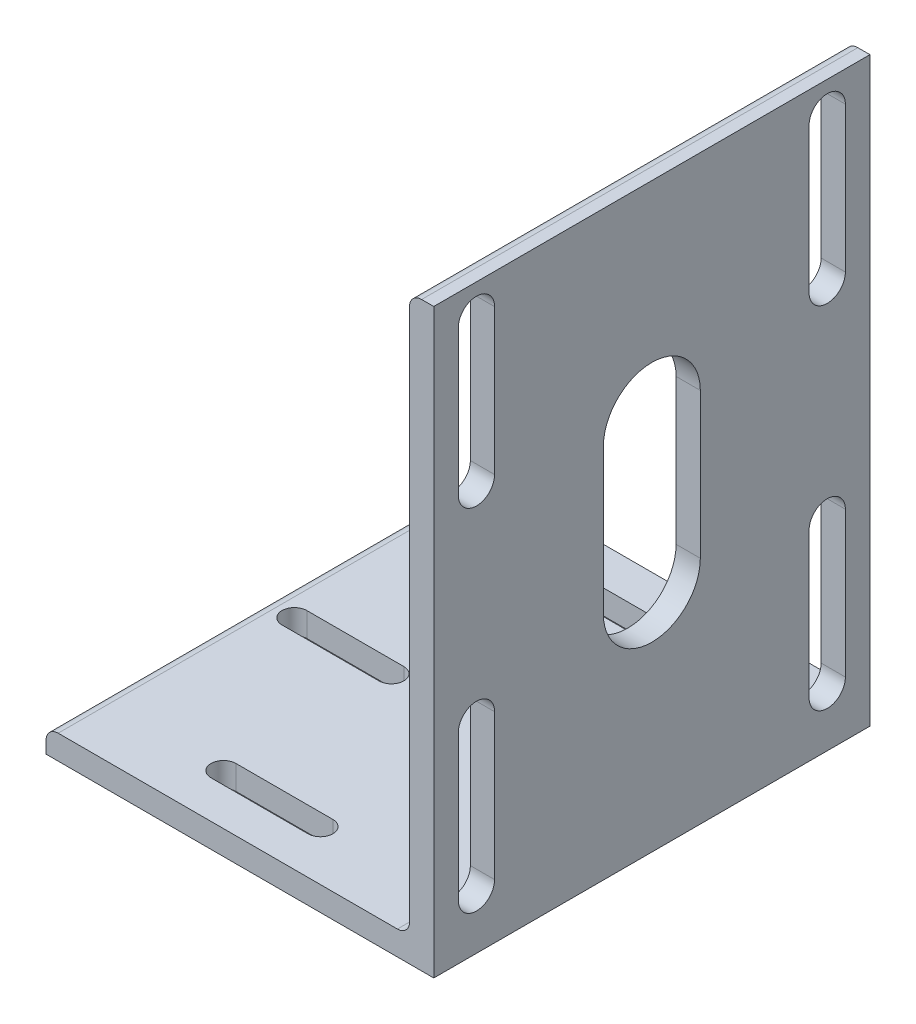
SolidWorks part; units mm, degrees
ref_plane "Front Plane" through (0, 0, 0) normal (0, 0, 1) x (1, 0, 0)
ref_plane "Top Plane" through (0, 0, 0) normal (0, 1, 0) x (1, 0, 0)
ref_plane "Right Plane" through (0, 0, 0) normal (1, 0, 0) x (0, 0, -1)
sketch "Sketch2" plane through (0, 0, 0) normal (0, 0, 1) x (1, 0, 0)
  line L0 (-50.8, 0) -> (50.8, 0)
  line L1 (50.8, 0) -> (50.8, 152.4)
  line L2 (50.8, 152.4) -> (44.45, 152.4) construction
  line L3 (44.45, 149.225) -> (44.45, 9.525)
  line L4 (41.275, 6.35) -> (-47.625, 6.35)
  line L5 (-50.8, 0) -> (-50.8, 6.35) construction
  line L6 (47.625, 152.4) -> (50.8, 152.4)
  line L7 (-50.8, 3.175) -> (-50.8, 0)
  arc A0 (44.45, 149.225) -> (47.625, 152.4) centre (47.625, 149.225) cw
  arc A1 (-50.8, 3.175) -> (-47.625, 6.35) centre (-47.625, 3.175) cw
  arc A2 (44.45, 9.525) -> (41.275, 6.35) centre (41.275, 9.525) cw
  dimension "Vert" = 152.4
  dimension "Horz" = 101.6
  dimension "Thickness" = 6.35
extrude "Boss-Extrude1" add sketch "Sketch2" along normal mid plane 304.8
ref_plane "Contact Plane 1" through (0, 6.35, 0) normal (0, 1, 0) x (1, 0, 0)
ref_plane "Contact Plane 2" through (44.45, 0, 0) normal (-1, 0, 0) x (0, 0, 1)
ref_plane "Plane1" through (0, 0, -38.1) normal (0, 0, -1) x (-1, 0, 0)
other "SurfaceCut1"
sketch "Sketch3" plane through (50.8, 0, 0) normal (1, 0, 0) x (0, 0, -1)
  line L0 (152.4, 79.375) -> (95.25, 79.375) construction
  line L1 (152.4, 0) -> (152.4, 152.4) construction
  line L2 (95.25, 79.375) -> (38.1, 79.375) construction
  line L3 (38.1, 152.4) -> (38.1, 0) construction
  line L4 (95.25, 152.4) -> (95.25, 6.35) construction
  line L5 (38.1, 152.4) -> (152.4, 152.4) construction
  line L6 (95.25, 79.375) -> (49.2881, 33.4131) construction
  line L7 (141.2119, 144.3869) -> (141.2119, 106.2869) construction
  line L8 (145.9619, 144.3869) -> (145.9619, 106.2869)
  line L9 (136.4619, 144.3869) -> (136.4619, 106.2869)
  line L10 (141.2119, 52.4631) -> (141.2119, 14.3631) construction
  line L11 (145.9619, 52.4631) -> (145.9619, 14.3631)
  line L12 (136.4619, 52.4631) -> (136.4619, 14.3631)
  line L13 (141.2119, 125.3369) -> (95.25, 79.375) construction
  line L14 (95.25, 79.375) -> (141.2119, 33.4131) construction
  line L15 (49.2881, 125.3369) -> (95.25, 79.375) construction
  line L16 (49.2881, 52.4631) -> (49.2881, 14.3631) construction
  line L17 (44.5381, 52.4631) -> (44.5381, 14.3631)
  line L18 (54.0381, 52.4631) -> (54.0381, 14.3631)
  line L19 (49.2881, 144.3869) -> (49.2881, 106.2869) construction
  line L20 (44.5381, 144.3869) -> (44.5381, 106.2869)
  line L21 (54.0381, 144.3869) -> (54.0381, 106.2869)
  line L22 (95.25, 98.425) -> (95.25, 60.325) construction
  line L23 (107.95, 98.425) -> (107.95, 60.325)
  line L24 (82.55, 98.425) -> (82.55, 60.325)
  circle A0 centre (95.25, 79.375) radius 65 construction
  arc A1 (145.9619, 144.3869) -> (136.4619, 144.3869) centre (141.2119, 144.3869) ccw
  arc A2 (136.4619, 106.2869) -> (145.9619, 106.2869) centre (141.2119, 106.2869) ccw
  arc A3 (145.9619, 52.4631) -> (136.4619, 52.4631) centre (141.2119, 52.4631) ccw
  arc A4 (136.4619, 14.3631) -> (145.9619, 14.3631) centre (141.2119, 14.3631) ccw
  arc A5 (44.5381, 52.4631) -> (54.0381, 52.4631) centre (49.2881, 52.4631) cw
  arc A6 (54.0381, 14.3631) -> (44.5381, 14.3631) centre (49.2881, 14.3631) cw
  arc A7 (44.5381, 144.3869) -> (54.0381, 144.3869) centre (49.2881, 144.3869) cw
  arc A8 (54.0381, 106.2869) -> (44.5381, 106.2869) centre (49.2881, 106.2869) cw
  arc A9 (107.95, 98.425) -> (82.55, 98.425) centre (95.25, 98.425) ccw
  arc A10 (82.55, 60.325) -> (107.95, 60.325) centre (95.25, 60.325) ccw
  point P14 (141.2119, 125.3369)
  point P17 (95.25, 79.375)
  point P22 (141.2119, 33.4131)
  point P34 (49.2881, 33.4131)
  point P41 (49.2881, 125.3369)
  point P48 (95.25, 79.375)
  dimension "D1" = 130
  dimension "D3" = 4.75
  dimension "D5" = 12.7
  dimension "D2" = 6.35
  dimension "D4" = 38.1
  dimension "D6" = 38.1
extrude "Cut-Extrude1" cut sketch "Sketch3" against normal through all
ref_plane "Plane2" through (0, 0, -95.25) normal (0, 0, -1) x (-1, 0, 0)
sketch "Sketch4" plane through (0, 6.35, 0) normal (0, 1, 0) x (1, 0, 0)
  line L0 (41.275, 95.25) -> (-50.8, 95.25) construction
  line L1 (41.275, 38.1) -> (41.275, 152.4) construction
  line L2 (-50.8, 38.1) -> (-50.8, 152.4) construction
  line L3 (-42.8625, 95.25) -> (-17.4625, 95.25) construction
  line L4 (-42.8625, 98.5139) -> (-17.4625, 98.5139)
  line L5 (-42.8625, 91.9861) -> (-17.4625, 91.9861)
  line L6 (7.9375, 95.25) -> (33.3375, 95.25) construction
  line L7 (7.9375, 98.5139) -> (33.3375, 98.5139)
  line L8 (7.9375, 91.9861) -> (33.3375, 91.9861)
  line L9 (-17.4625, 139.2441) -> (7.9375, 139.2441) construction
  line L10 (-17.4625, 142.508) -> (7.9375, 142.508)
  line L11 (-17.4625, 135.9802) -> (7.9375, 135.9802)
  line L12 (-17.4625, 51.2559) -> (7.9375, 51.2559) construction
  line L13 (-17.4625, 47.992) -> (7.9375, 47.992)
  line L14 (-17.4625, 54.5198) -> (7.9375, 54.5198)
  arc A1 (-42.8625, 98.5139) -> (-42.8625, 91.9861) centre (-42.8625, 95.25) ccw
  arc A2 (-17.4625, 91.9861) -> (-17.4625, 98.5139) centre (-17.4625, 95.25) ccw
  arc A3 (7.9375, 98.5139) -> (7.9375, 91.9861) centre (7.9375, 95.25) ccw
  arc A4 (33.3375, 91.9861) -> (33.3375, 98.5139) centre (33.3375, 95.25) ccw
  arc A5 (-17.4625, 142.508) -> (-17.4625, 135.9802) centre (-17.4625, 139.2441) ccw
  arc A6 (7.9375, 135.9802) -> (7.9375, 142.508) centre (7.9375, 139.2441) ccw
  arc A7 (-17.4625, 47.992) -> (-17.4625, 54.5198) centre (-17.4625, 51.2559) cw
  arc A8 (7.9375, 54.5198) -> (7.9375, 47.992) centre (7.9375, 51.2559) cw
  point P8 (-30.1625, 95.25)
  point P15 (20.6375, 95.25)
  point P20 (-4.7625, 139.2441)
  point P23 (-4.7625, 139.2441)
  point P30 (-4.7625, 51.2559)
  point P36 (-4.7625, 95.25)
  dimension "D1" = 6.5278
  dimension "D2" = 25.4
  dimension "D4" = 50.8
  dimension "D5" = 25.4
  dimension "D6" = 50.8
extrude "Cut-Extrude2" cut sketch "Sketch4" against normal through all
